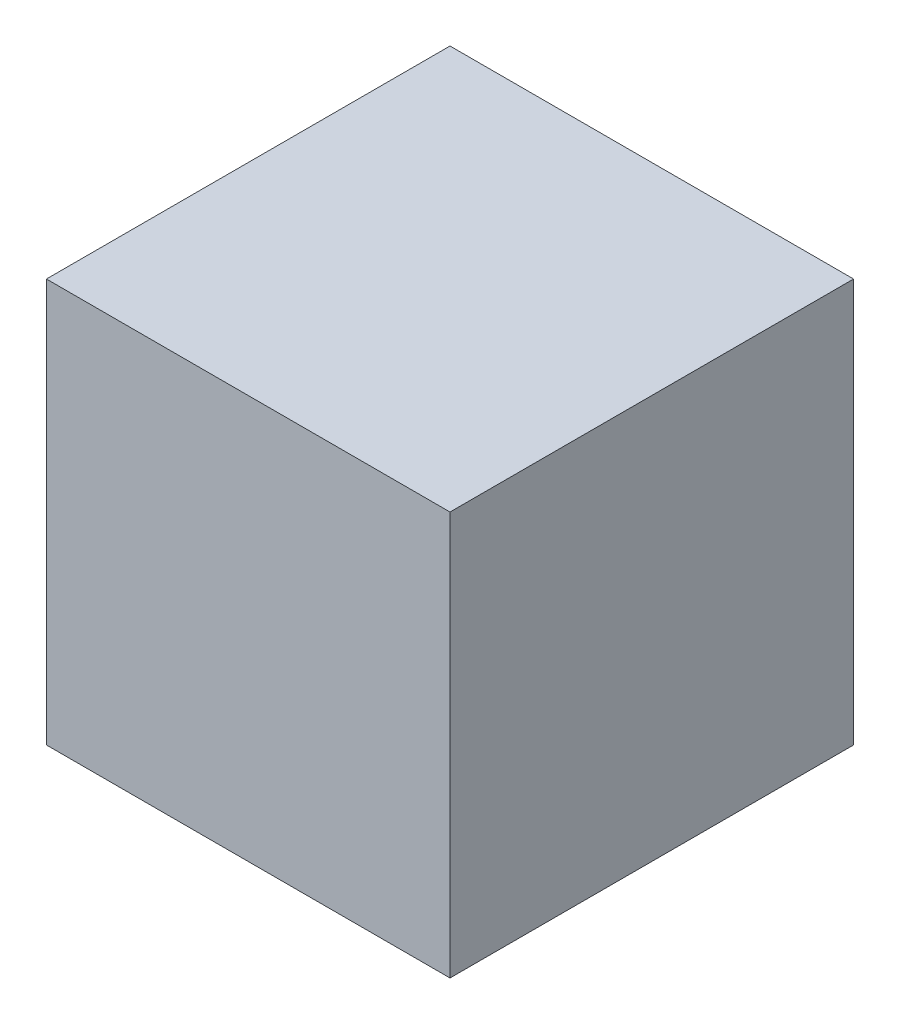
SolidWorks part; units mm, degrees
ref_plane "Front Plane" through (0, 0, 0) normal (0, 0, 1) x (1, 0, 0)
ref_plane "Top Plane" through (0, 0, 0) normal (0, 1, 0) x (1, 0, 0)
ref_plane "Right Plane" through (0, 0, 0) normal (1, 0, 0) x (0, 0, -1)
sketch "Sketch1" plane through (0, 0, 0) normal (0, 1, 0) x (1, 0, 0)
  line L1 (0, -42) -> (0, 42) construction
  line L2 (-60, -48.8988) -> (-60, 48.8988) construction
  line L3 (60, -48.8988) -> (60, 48.8988) construction
  line L4 (41.2438, 60) -> (-41.2438, 60) construction
  line L5 (45.0878, -60) -> (-45.0878, -60) construction
  line L6 (45.0878, 0) -> (-45.0878, 0) construction
  point P3 (0, 0)
  point P7 (0, 0)
  point P11 (-60, 0)
  point P14 (60, 0)
  point P17 (0, 60)
  point P20 (0, -60)
  dimension "D1" = 60
  dimension "D2" = 60
  dimension "D3" = 60
  dimension "D4" = 60
  dimension "D5" = 84
sketch "Sketch2" [suppressed] plane through (0, 0, 0) normal (0, 0, 1) x (1, 0, 0)
  line L0 (-60, -42) -> (-60, 42) construction
  line L1 (0, -42) -> (0, 42) construction
  line L3 (60, -42) -> (60, 42) construction
  point P4 (-60, 0)
  point P8 (0, 0)
  point P12 (60, 0)
  dimension "D1" = 84
ref_plane "Plane1" through (0, 30, 0) normal (0, 1, 0) x (1, 0, 0)
sketch "Sketch3" plane through (0, 30, 0) normal (0, 1, 0) x (1, 0, 0)
  line L0 (0, -42) -> (0, 42) construction
  line L1 (0, 0) -> (-10, 0)
  line L2 (0, 0) -> (0, -10)
  line L3 (0, -10) -> (-10, -10)
  line L4 (-10, 0) -> (-10, -10)
  dimension "D1" = 10
extrude "Cube" add sketch "Sketch3" along normal blind 10
